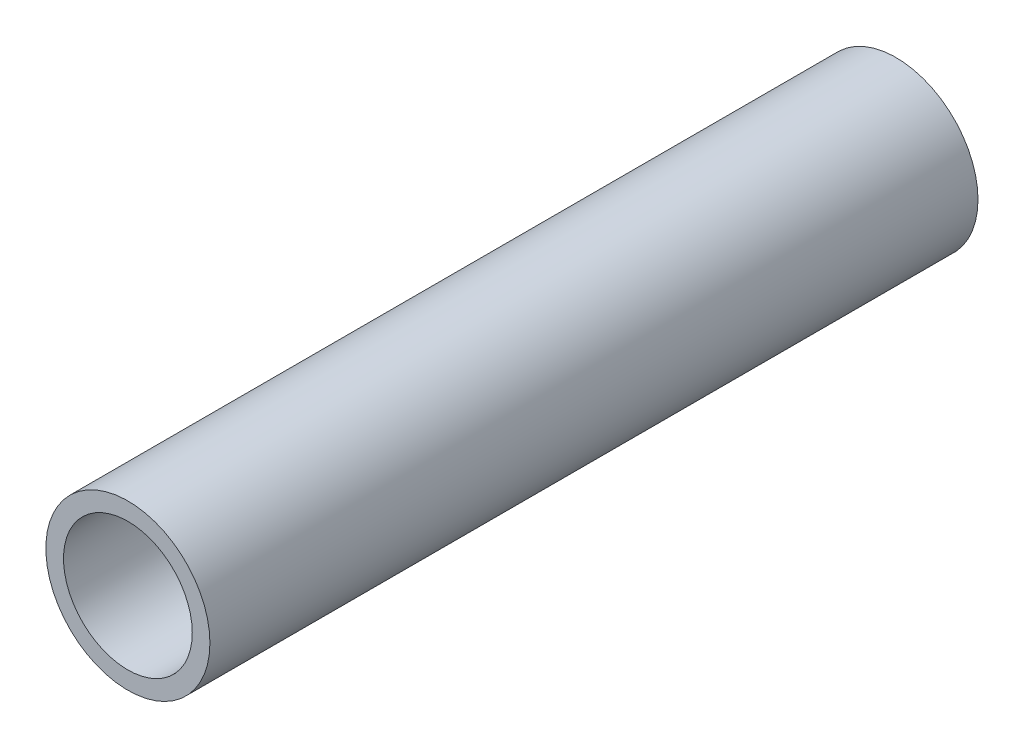
SolidWorks part; units mm, degrees
material "PVC 0.007 Plasticized"
ref_plane "Front Plane" through (0, 0, 0) normal (0, 0, 1) x (1, 0, 0)
ref_plane "Top Plane" through (0, 0, 0) normal (0, 1, 0) x (1, 0, 0)
ref_plane "Right Plane" through (0, 0, 0) normal (1, 0, 0) x (0, 0, -1)
sketch "Sketch1" plane through (0, 0, 0) normal (0, 0, 1) x (1, 0, 0)
  line L0 (10.4648, 0) -> (13.335, 0) construction
  circle A0 centre (0, 0) radius 13.335 construction
  circle A1 centre (0, 0) radius 10.4648 construction
  dimension "ID" = 20.9296
  dimension "OD" = 26.67
  dimension "Wall Thickness" = 2.8702
sketch "Sketch2" plane through (0, 0, 0) normal (1, 0, 0) x (0, 0, -1)
  line L0 (-762, 0) -> (762, 0) construction
  line L1 (-728.6625, 13.335) -> (-728.6625, -13.335) construction
  line L2 (728.6625, 13.335) -> (728.6625, -13.335) construction
  point P4 (0, 0)
  point P8 (-728.6625, 0)
  point P11 (728.6625, 0)
  dimension "Length" = 1524
  dimension "D1" = 33.3375
  dimension "D2" = 33.3375
  dimension "D3" = 26.67
sketch "Sketch3" plane through (0, 0, 0) normal (0, 0, 1) x (1, 0, 0)
  circle A0 centre (0, 0) radius 13.335
  circle A1 centre (0, 0) radius 13.335 construction
  circle A2 centre (0, 0) radius 10.4648 construction
  circle A3 centre (0, 0) radius 10.4648
extrude "Boss-Extrude1" add sketch "Sketch3" along normal up to vertex (762 mm away) and the other way up to vertex (762 mm away) up to point (0, 0, 762) other way up to point (0, 0, -762)
sketch "Sketch4" plane through (0, 0, 762) normal (0, 0, 1) x (1, 0, 0)
  circle A0 centre (0, 0) radius 10.4648 construction
  circle A1 centre (0, 0) radius 13.335 construction
  circle A2 centre (0, 0) radius 10.4648
  circle A3 centre (0, 0) radius 13.335
extrude "Cut-Extrude2" cut sketch "Sketch4" against normal offset from surface (1399.1555 mm away) 124.8445 contours A3 up to face at (10.4648, 0, -762)
equation "\"D1@Sketch2\"=\"OD@Sketch1\" * 1.25"
equation "\"D2@Sketch2\"=\"D1@Sketch2\""
equation "\"D3@Sketch2\"= \"OD@Sketch1\""
